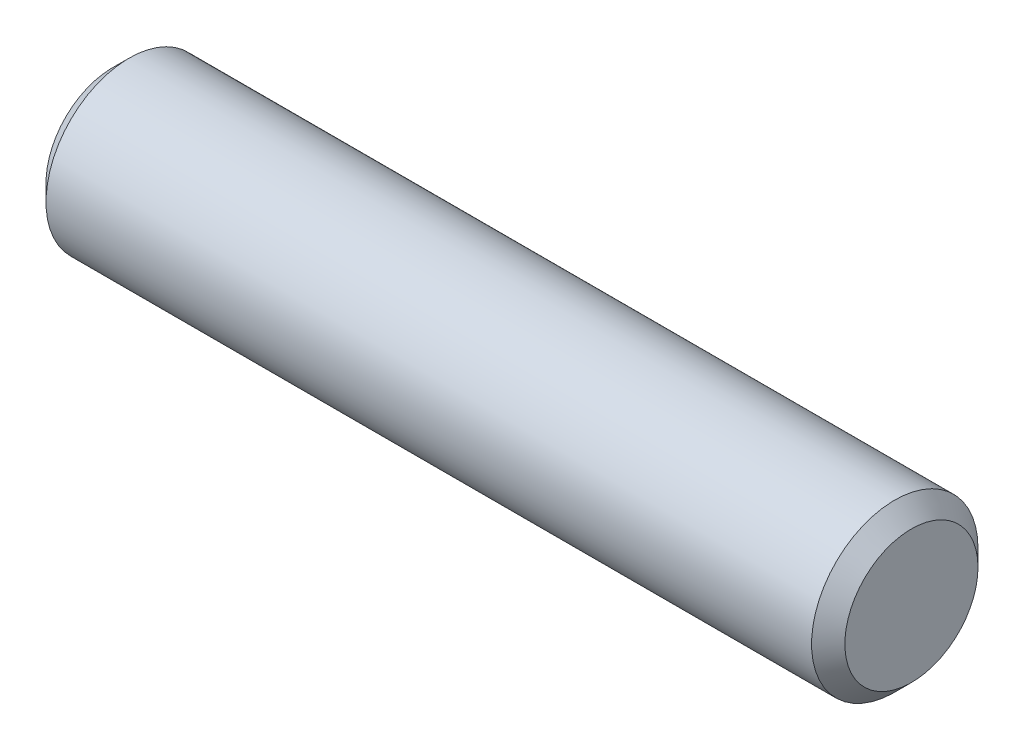
SolidWorks part; units mm, degrees
ref_plane "Front Plane" through (0, 0, 0) normal (0, 0, 1) x (1, 0, 0)
ref_plane "Top Plane" through (0, 0, 0) normal (0, 1, 0) x (1, 0, 0)
ref_plane "Right Plane" through (0, 0, 0) normal (1, 0, 0) x (0, 0, -1)
sketch "Sketch1" plane through (0, 0, 0) normal (0, 0, 1) x (1, 0, 0)
  line L0 (-19.05, 0) -> (19.05, 0) construction
  line L1 (-19.05, 3.9688) -> (-19.05, -3.9688) construction
  line L2 (19.05, 3.9688) -> (19.05, -3.9688) construction
  dimension "Diameter" = 7.9375
  dimension "Length" = 38.1
sketch "Sketch2" plane through (0, 0, 0) normal (1, 0, 0) x (0, 0, -1)
  circle A0 centre (0, 0) radius 3.9688
extrude "Extrude1" add sketch "Sketch2" against normal up to vertex (19.05 mm away) and the other way up to vertex (19.05 mm away) up to point (-19.05, 0, 0) other way up to point (19.05, 0, 0)
chamfer "Chamfer1" distance 0.7937 angle 45 2 edges at (19.05, 0, -3.9688) (-19.05, 0, -3.9688)
equation "\"D1@Chamfer1\" = \"Diameter@Sketch1\"*.1"
